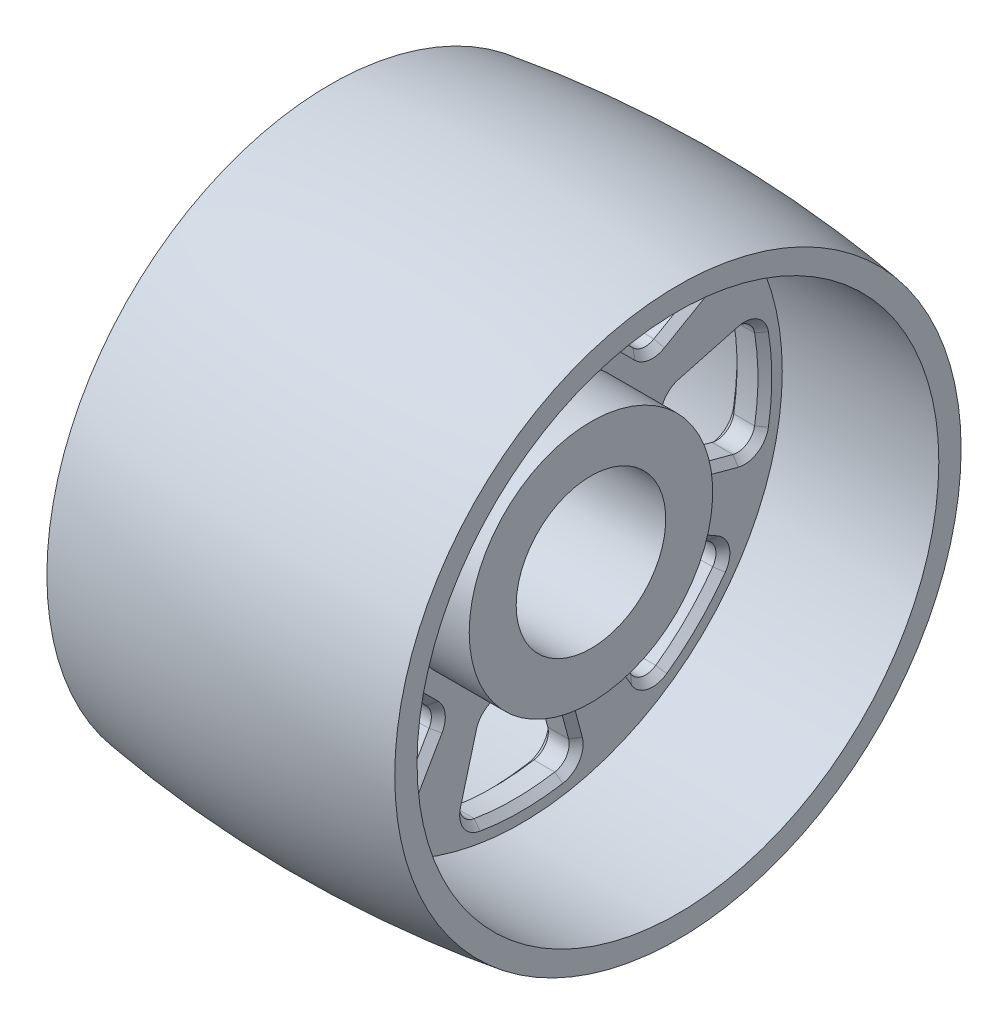
SolidWorks part; units mm, degrees
ref_plane "Front Plane" through (0, 0, 0) normal (0, 0, 1) x (1, 0, 0)
ref_plane "Top Plane" through (0, 0, 0) normal (0, 1, 0) x (1, 0, 0)
ref_plane "Right Plane" through (0, 0, 0) normal (1, 0, 0) x (0, 0, -1)
sketch "Sketch1" plane through (0, 0, 0) normal (0, 0, 1) x (1, 0, 0)
  line L0 (0, 0) -> (115.6071, 0) construction
  line L1 (0, 0) -> (0, 64.5539) construction
  line L2 (-50, 43) -> (50, 43)
  line L3 (-50, 43) -> (-50, 70)
  line L4 (-50, 70) -> (-10, 70)
  line L5 (-10, 70) -> (-10, 150)
  line L6 (-10, 150) -> (-100, 150)
  line L7 (-100, 150) -> (-100, 162.8203)
  line L8 (100, 150) -> (100, 162.8203)
  line L9 (10, 150) -> (100, 150)
  line L10 (10, 70) -> (10, 150)
  line L11 (50, 70) -> (10, 70)
  line L12 (50, 43) -> (50, 70)
  arc A0 (-100, 162.8203) -> (100, 162.8203) centre (0, -530) cw
  point P17 (0, 170)
  point P18 (-30.8461, 57.5709)
  point P19 (-330.7672, 86.9223)
  point P20 (-330.7672, 72.2498)
  point P21 (-138.0268, 156.257)
  point P22 (-73.6613, 136.0178)
  point P23 (-16.2313, 85.897)
  point P24 (0, 64.5539)
  dimension "D3" = 700
  dimension "D1" = 100
  dimension "D2" = 43
  dimension "D4" = 170
  dimension "D5" = 200
  dimension "D6" = 150
  dimension "D7" = 20
  dimension "D8" = 70
revolve "Revolve1" add sketch "Sketch1" angle 360 about L0
sketch "Sketch2" plane through (10, 0, 0) normal (1, 0, 0) x (0, 0, -1)
  line L0 (0, 0) -> (0, 150) construction
  line L1 (-20, 84) -> (20, 84)
  line L3 (20, 84) -> (33.8895, 135.8363)
  line L4 (-20, 84) -> (-33.8895, 135.8363)
  circle A0 centre (0, 0) radius 150 construction
  arc A1 (-33.8895, 135.8363) -> (33.8895, 135.8363) centre (0, 0) cw
  point P11 (38.2762, 129.6417)
  point P12 (0, 0)
  dimension "D3" = 140
  dimension "D1" = 84
  dimension "D2" = 40
  dimension "D4" = 30
extrude "Cut-Extrude1" cut sketch "Sketch2" against normal up to next (20 mm away)
fillet "Fillet1" radius 10 4 edges at (0, 135.8363, 33.8895) (0, 135.8363, -33.8895) (0, 84, -20) (0, 84, 20)
chamfer "Chamfer1" distance 4 angle 45 16 edges at (10, 108.5172, -26.5694) (10, 133.6194, -29.9047) (10, 86.0665, -18.4143) (10, 140, 0) (10, 84, 0) (10, 133.6194, 29.9047) (10, 86.0665, 18.4143) (10, 108.5172, 26.5694) (-10, 108.5172, -26.5694) (-10, 86.0665, -18.4143) (-10, 133.6194, -29.9047) (-10, 84, 0) (-10, 140, 0) (-10, 86.0665, 18.4143) (-10, 133.6194, 29.9047) (-10, 108.5172, 26.5694)
pattern_circular "CirPattern1" count 8 over 360 about axis through (0, 0, 0) along (1, 0, 0) of "Cut-Extrude1", "Fillet1", "Chamfer1"
